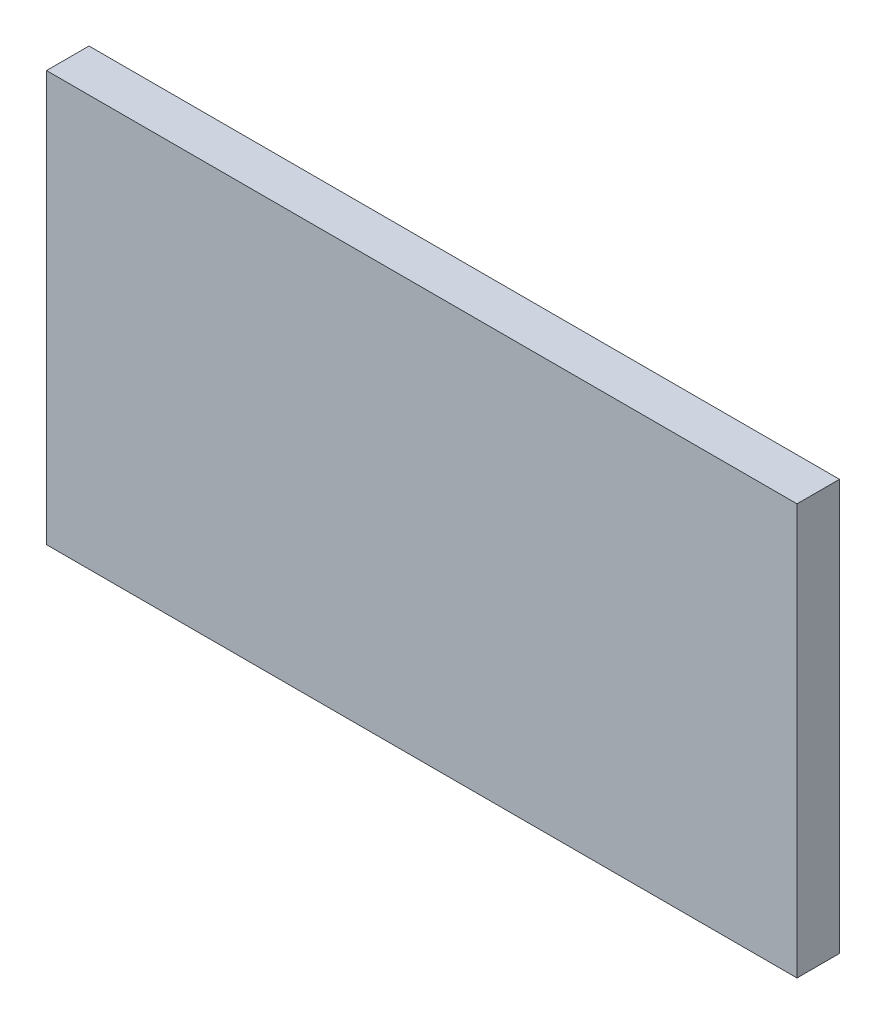
SolidWorks part; units mm, degrees
material "ABS PC"
ref_plane "Front Plane" through (0, 0, 0) normal (0, 0, 1) x (1, 0, 0)
ref_plane "Top Plane" through (0, 0, 0) normal (0, 1, 0) x (1, 0, 0)
ref_plane "Right Plane" through (0, 0, 0) normal (1, 0, 0) x (0, 0, -1)
sketch "Sketch1" plane through (0, 0, 204.7871) normal (0, 0, 1) x (1, 0, 0)
  line L7 (-507.2472, -467.8127) -> (-493.7852, -467.8127)
  line L8 (-493.7852, -467.8127) -> (-493.7852, -475.1787)
  line L9 (-507.2472, -475.1787) -> (-493.7852, -475.1787)
  line L10 (-507.2472, -467.8127) -> (-507.2472, -475.1787)
  dimension "D1" = 13.462
  dimension "D2" = 7.366
extrude "Boss-Extrude1" add sketch "Sketch1" along normal blind 0.762
